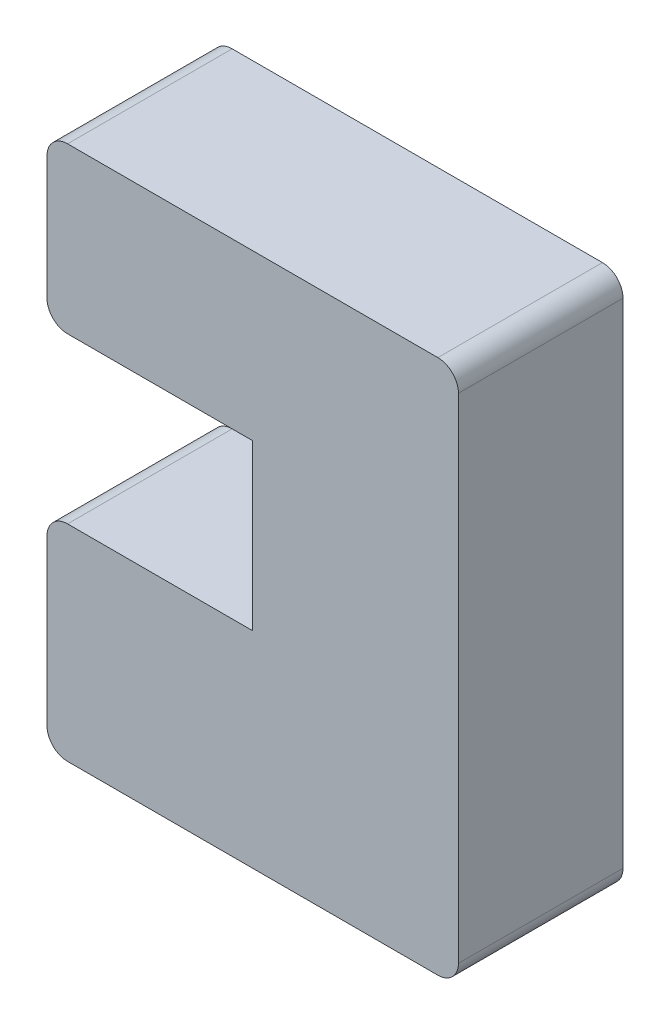
SolidWorks part; units mm, degrees
ref_plane "Front Plane" through (0, 0, 0) normal (0, 0, 1) x (1, 0, 0)
ref_plane "Top Plane" through (0, 0, 0) normal (0, 1, 0) x (1, 0, 0)
ref_plane "Right Plane" through (0, 0, 0) normal (1, 0, 0) x (0, 0, -1)
sketch "Sketch1" plane through (0, 0, 0) normal (0, 0, 1) x (1, 0, 0)
  line L0 (1, 0) -> (19, 0)
  line L1 (20, 1) -> (20, 25)
  line L2 (19, 26) -> (1, 26)
  line L3 (0, 25) -> (0, 19)
  line L4 (1, 18) -> (10, 18)
  line L5 (10, 18) -> (10, 10)
  line L6 (10, 10) -> (1, 10)
  line L7 (0, 9) -> (0, 1)
  arc A0 (1, 10) -> (0, 9) centre (1, 9) ccw
  arc A1 (0, 1) -> (1, 0) centre (1, 1) ccw
  arc A2 (19, 0) -> (20, 1) centre (19, 1) ccw
  arc A3 (20, 25) -> (19, 26) centre (19, 25) ccw
  arc A4 (0, 25) -> (1, 26) centre (1, 25) cw
  arc A5 (0, 19) -> (1, 18) centre (1, 19) ccw
  point P13 (0, 0)
  point P16 (20, 0)
  dimension "D6" = 1
  dimension "D1" = 20
  dimension "D2" = 10
  dimension "D3" = 8
  dimension "D4" = 8
  dimension "D5" = 10
extrude "Boss-Extrude1" add sketch "Sketch1" along normal blind 8
